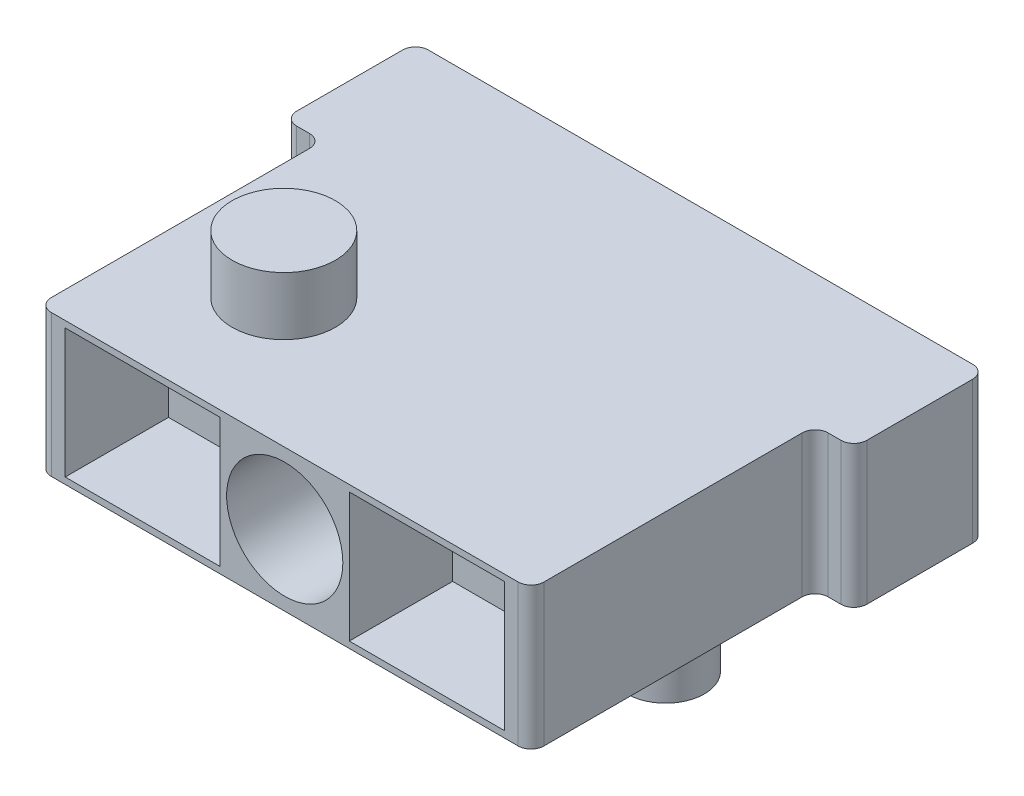
SolidWorks part; units mm, degrees
ref_plane "前基準面" through (0, 0, 0) normal (0, 0, 1) x (1, 0, 0)
ref_plane "上基準面" through (0, 0, 0) normal (0, 1, 0) x (1, 0, 0)
ref_plane "右基準面" through (0, 0, 0) normal (1, 0, 0) x (0, 0, -1)
sketch "草圖2" plane through (0, 0, 0) normal (0, 0, 1) x (1, 0, 0)
  line L0 (-98.7451, 53.1438) -> (5.0716, 53.1438) construction
  line L10 (-22.075, -5.5) -> (22.075, -5.5)
  line L11 (-22.075, -5.5) -> (-22.075, 5.5)
  line L12 (-22.075, 5.5) -> (22.075, 5.5)
  line L13 (22.075, -5.5) -> (22.075, 5.5)
  line L14 (-22.075, -5.5) -> (22.075, 5.5) construction
  line L15 (-22.075, 5.5) -> (22.075, -5.5) construction
  point P2 (0, 0)
  dimension "D1" = 11
  dimension "D2" = 44.15
extrude "填料-伸長1" add sketch "草圖2" against normal blind 32.2
sketch "草圖3" plane through (0, -5.5, 0) normal (0, -1, 0) x (1, 0, 0)
  line L0 (-14.3, -15.2) -> (14.3, -15.2) construction
  line L1 (-22.075, -32.2) -> (22.075, -32.2) construction
  line L2 (0, -15.2) -> (0, -32.2) construction
  circle A0 centre (-14.3, -15.2) radius 3
  circle A1 centre (14.3, -15.2) radius 3
  dimension "D2" = 6
  dimension "D1" = 17
  dimension "D3" = 28.6
extrude "填料-伸長2" add sketch "草圖3" along normal blind 4.5
hole_wizard "M3x0.5  螺絲攻的螺孔鑽1" positions "草圖4" profile "草圖6" hole size "M3x0.5" standard "Ansi Metric"
sketch "草圖4" plane through (0, -10, 0) normal (0, -1, 0) x (-1, 0, 0)
  circle A0 centre (14.3, 15.2) radius 3 construction
  point P0 (14.3, 15.2)
  point P2 (-14.3, 15.2)
  point P6 (14.5072, 15.2)
  point P7 (14.3241, 15.2)
sketch "草圖6" plane through (-14.3, -10, -15.2) normal (1, 0, 0) x (0, 0, -1)
  line L0 (0, 0) -> (0, 5.7511)
  line L1 (0, 5.7511) -> (1.25, 5)
  line L2 (1.25, 5) -> (1.25, 0)
  line L5 (1.25, 0) -> (0, 0)
  line L10 (0, 5.7511) -> (-1.25, 5) construction
  line L11 (0, -6.35) -> (0, 107.95) construction
  dimension "鑽孔直徑" = 2.5
  dimension "鑽孔深度" = 5
  dimension "導頭角度" = 118
sketch "草圖7" plane through (0, 5.5, 0) normal (0, 1, 0) x (1, 0, 0)
  line L0 (22.075, 0) -> (-22.075, 0) construction
  line L1 (-22.075, 32.2) -> (-22.075, 0) construction
  circle A0 centre (-10.075, 10) radius 4
  point P6 (-21.5645, 7.2359)
  dimension "D1" = 8
  dimension "D2" = 10
  dimension "D3" = 12
extrude "填料-伸長3" add sketch "草圖7" along normal blind 4.5
sketch "草圖8" plane through (0, 5.5, 0) normal (0, 1, 0) x (1, 0, 0)
  line L1 (-22.075, 0) -> (-19.075, 0)
  line L2 (-22.075, 0) -> (-22.075, 22)
  line L3 (-22.075, 22) -> (-19.075, 22)
  line L4 (-19.075, 0) -> (-19.075, 22)
  line L5 (22.075, 0) -> (19.075, 0)
  line L6 (22.075, 0) -> (22.075, 22)
  line L7 (22.075, 22) -> (19.075, 22)
  line L8 (19.075, 0) -> (19.075, 22)
  dimension "D1" = 38.15
  dimension "D2" = 22
extrude "除料-伸長1" cut sketch "草圖8" against normal through all
sketch "草圖9" plane through (0, 0, 0) normal (0, 0, 1) x (1, 0, 0)
  line L0 (-19.075, 0) -> (19.075, 0) construction
  line L1 (-17, 5) -> (-5, 5)
  line L2 (-17, 5) -> (-17, -5)
  line L3 (-17, -5) -> (-5, -5)
  line L4 (-5, 5) -> (-5, -5)
  line L5 (5, 5) -> (17, 5)
  line L6 (5, 5) -> (5, -5)
  line L7 (5, -5) -> (17, -5)
  line L8 (17, 5) -> (17, -5)
  line L9 (-19.075, 5.5) -> (-19.075, -5.5) construction
  line L10 (19.075, -5.5) -> (19.075, 5.5) construction
  line L11 (0, 5.5) -> (0, -5.5) construction
  line L12 (19.075, 5.5) -> (-19.075, 5.5) construction
  line L13 (-19.075, -5.5) -> (19.075, -5.5) construction
  dimension "D1" = 12
  dimension "D2" = 10
  dimension "D3" = 10
extrude "除料-伸長2" cut sketch "草圖9" against normal blind 8
sketch "草圖10" plane through (0, 0, 0) normal (0, 0, 1) x (1, 0, 0)
  circle A0 centre (0, 0) radius 4.5
  dimension "D1" = 9
extrude "除料-伸長3" cut sketch "草圖10" against normal blind 10
fillet "圓角1" radius 1 8 edges at (22.075, 0, -32.2) (-22.075, 0, -32.2) (-22.075, 0, -22) (22.075, 0, -22) (19.075, 0, 0) (-19.075, 0, 0) (-19.075, 0, -22) (19.075, 0, -22)
